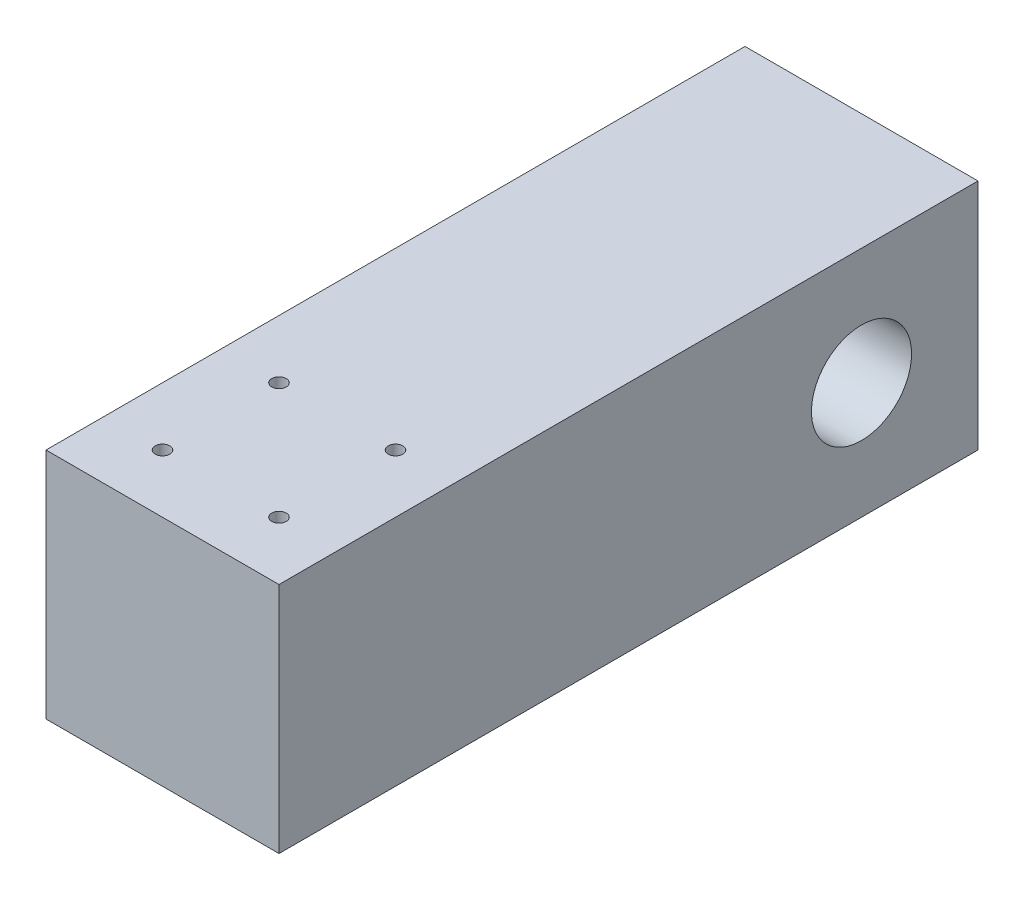
SolidWorks part; units mm, degrees
material "Pine"
ref_plane "Front Plane" through (0, 0, 0) normal (0, 0, 1) x (1, 0, 0)
ref_plane "Top Plane" through (0, 0, 0) normal (0, 1, 0) x (1, 0, 0)
ref_plane "Right Plane" through (0, 0, 0) normal (1, 0, 0) x (0, 0, -1)
sketch "Sketch1" plane through (0, 0, 0) normal (1, 0, 0) x (0, 0, -1)
  line L1 (0, 0) -> (152.4, 0)
  line L2 (0, 0) -> (0, 50.8)
  line L3 (0, 50.8) -> (152.4, 50.8)
  line L4 (152.4, 0) -> (152.4, 50.8)
  dimension "D1" = 50.8
  dimension "D2" = 152.4
extrude "Boss-Extrude1" add sketch "Sketch1" along normal blind 50.8
sketch "Sketch2" plane through (50.8, 0, 0) normal (1, 0, 0) x (0, 0, -1)
  line L0 (152.4, 0) -> (152.4, 50.8) construction
  line L1 (152.4, 50.8) -> (0, 50.8) construction
  circle A0 centre (127, 25.4) radius 10.9141
  dimension "D1" = 21.8281
  dimension "D2" = 25.4
  dimension "D3" = 25.4
extrude "Cut-Extrude1" cut sketch "Sketch2" against normal through all
sketch "Sketch3" plane through (0, 50.8, 0) normal (0, 1, 0) x (1, 0, 0)
  line L0 (0, 152.4) -> (0, 0) construction
  line L1 (50.8, 152.4) -> (50.8, 0) construction
  line L2 (50.8, 0) -> (0, 0) construction
  circle A0 centre (12.7, 38.1) radius 1.5875
  circle A1 centre (38.1, 38.1) radius 1.5875
  circle A2 centre (12.7, 12.7) radius 1.5875
  circle A3 centre (38.1, 12.7) radius 1.5875
  dimension "D1" = 3.175
  dimension "D2" = 12.7
  dimension "D4" = 12.7
  dimension "D5" = 12.7
  dimension "D6" = 12.7
  dimension "D7" = 12.7
  dimension "D8" = 25.4
  dimension "D9" = 25.4
  dimension "D3" = 12.7
extrude "Cut-Extrude2" cut sketch "Sketch3" against normal through all
